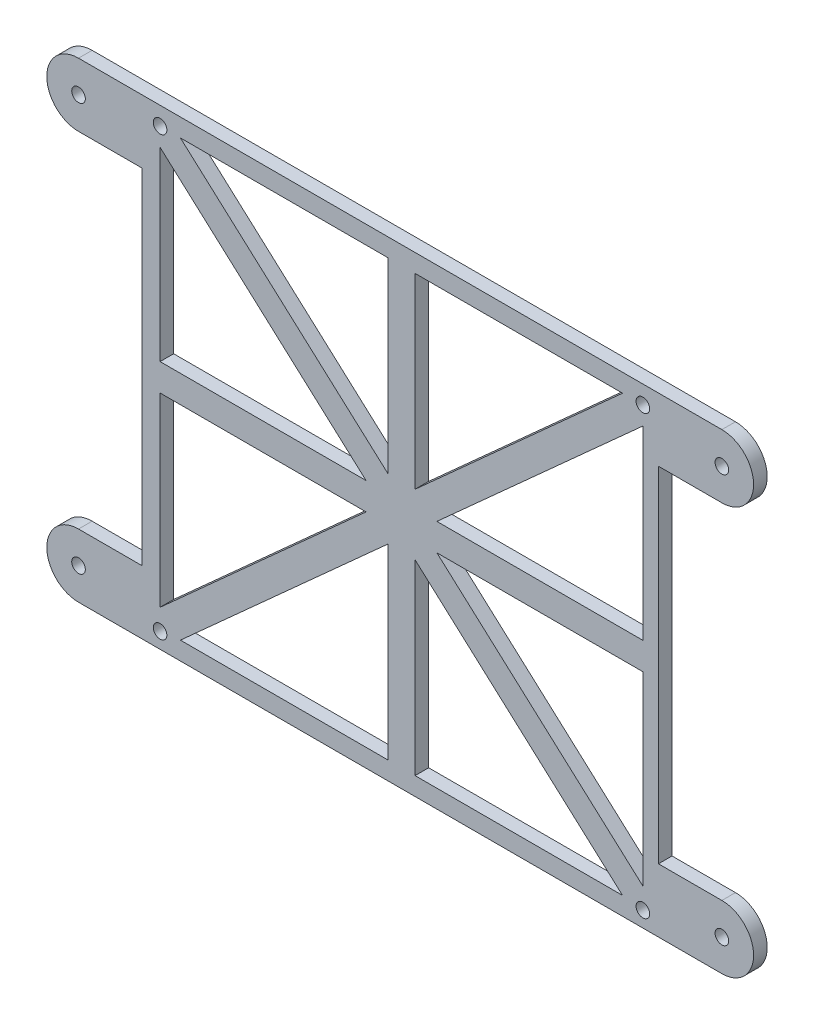
SolidWorks part; units mm, degrees
ref_plane "Front Plane" through (0, 0, 0) normal (0, 0, 1) x (1, 0, 0)
ref_plane "Top Plane" through (0, 0, 0) normal (0, 1, 0) x (1, 0, 0)
ref_plane "Right Plane" through (0, 0, 0) normal (1, 0, 0) x (0, 0, -1)
sketch "Sketch1" plane through (0, 0, 0) normal (0, 0, 1) x (1, 0, 0)
  line L0 (-53, 48) -> (53, -48) construction
  line L1 (-53, 48) -> (53, 48) construction
  line L2 (-53, 48) -> (-53, -48) construction
  line L3 (-53, -48) -> (53, -48) construction
  line L4 (53, 48) -> (53, -48) construction
  line L5 (0, 0) -> (0, 410.77) construction
  line L6 (0, 0) -> (665.5111, 0) construction
  point P5 (0, 0)
  dimension "D1" = 106
  dimension "D2" = 96
sketch "Sketch3" plane through (0, 0, 0) normal (0, 0, 1) x (1, 0, 0)
  line L14 (57, -52) -> (57, 52)
  line L15 (-57, -52) -> (57, -52)
  line L16 (-57, 52) -> (-57, -52)
  line L17 (57, 52) -> (-57, 52)
  line L18 (57, -52) -> (57, 52)
  line L19 (-57, -52) -> (57, -52)
  line L20 (-57, 52) -> (-57, -52)
  line L21 (57, 52) -> (-57, 52)
  dimension "D1" = 4
extrude "Boss-Extrude1" add sketch "Sketch3" along normal blind 3
sketch "Sketch4" plane through (0, 0, 3) normal (0, 0, 1) x (1, 0, 0)
  circle A0 centre (-53, 48) radius 1.5
  dimension "D1" = 3
extrude "Cut-Extrude1" cut sketch "Sketch4" against normal through all
pattern_linear "LPattern1" count 2 spacing 106.56 along (1, 0, 0) count 2 spacing 96.56 along (0, -1, 0) of "Cut-Extrude1"
sketch "Sketch5" plane through (0, 0, 3) normal (0, 0, 1) x (1, 0, 0)
  line L0 (-57, 52) -> (-71, 52)
  line L1 (-71, 38) -> (-57, 38)
  line L2 (-57, 52) -> (-57, -52) construction
  line L3 (-57, 38) -> (-57, 52)
  arc A0 (-71, 52) -> (-71, 38) centre (-71, 45) ccw
  dimension "D2" = 7
  dimension "D1" = 14
extrude "Boss-Extrude2" add sketch "Sketch5" against normal up to surface (3 mm away) up to face at (55.06, 48, 0)
sketch "Sketch6" plane through (0, 0, 3) normal (0, 0, 1) x (1, 0, 0)
  circle A0 centre (-71, 45) radius 1.5
  dimension "D1" = 3
extrude "Cut-Extrude2" cut sketch "Sketch6" against normal through all
mirror "Mirror1" about plane through (0, 0, 0) normal (0, 1, 0) of "Cut-Extrude2", "Boss-Extrude2" second plane through (0, 0, 0) second plane normal (1, 0, 0)
sketch "Sketch7" plane through (0, 0, 3) normal (0, 0, 1) x (1, 0, 0)
  line L0 (-53, 48) -> (53.56, -48) construction
  line L1 (53.56, 48) -> (-53, -48) construction
  line L2 (-53.28, 0) -> (53.56, 0) construction
  line L5 (-53.28, -3) -> (53.56, -3)
  line L6 (-55.008, 45.7711) -> (51.552, -50.2289)
  line L7 (51.552, 50.2289) -> (-55.008, -45.7711)
  line L8 (-53.28, 3) -> (53.56, 3)
  line L9 (-50.992, 50.2289) -> (55.568, -45.7711)
  line L10 (55.568, 45.7711) -> (-50.992, -50.2289)
  line L11 (0.28, 48) -> (0.28, -48)
  line L12 (-53, 48) -> (53.56, 48)
  line L13 (-53, 48) -> (-53, -48)
  line L14 (-53, -48) -> (53.56, -48)
  line L15 (53.56, 48) -> (53.56, -48)
  line L16 (-2.72, 48) -> (-2.72, -48)
  line L17 (3.28, 48) -> (3.28, -48)
  point P10 (0, 0)
  dimension "D1" = 3
  dimension "D2" = 3
  dimension "D3" = 3
  dimension "D4" = 3
extrude "Cut-Extrude3" cut sketch "Sketch7" against normal through all contours L16 L10 L14 | L6 L17 L14 | L15 L5 L9 | L15 L10 L8 | L12 L17 L7 | L16 L12 L9 | L6 L13 L8 | L5 L13 L7
